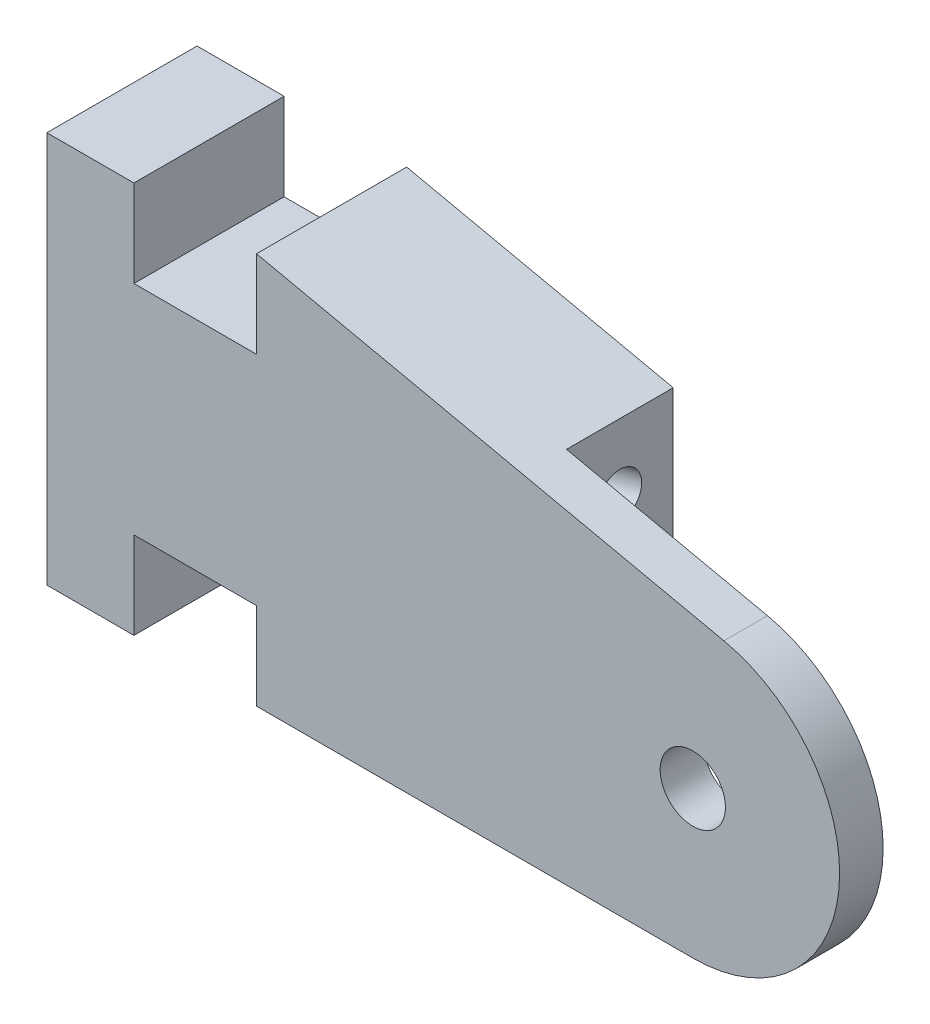
SolidWorks part; units mm, degrees
ref_plane "Front Plane" through (0, 0, 0) normal (0, 0, 1) x (1, 0, 0)
ref_plane "Top Plane" through (0, 0, 0) normal (0, 1, 0) x (1, 0, 0)
ref_plane "Right Plane" through (0, 0, 0) normal (1, 0, 0) x (0, 0, -1)
sketch "Sketch1" plane through (0, 0, 0) normal (0, 0, 1) x (1, 0, 0)
  line L0 (0, 0) -> (0, 18.0003)
  line L1 (9.6315, 0) -> (9.6315, 4)
  line L2 (9.6315, 4) -> (4, 4)
  line L3 (9.6315, 18.0003) -> (31.1079, 13.3365)
  line L4 (9.6315, 18.0003) -> (9.6315, 14.0003)
  line L5 (9.6315, 14.0003) -> (4, 14.0003)
  line L6 (0, 0) -> (4, 0)
  line L7 (4, 0) -> (4, 4)
  line L9 (14.2505, 12.0256) -> (12.2808, 11.6783) construction
  line L10 (7.3568, 10.81) -> (8.225, 5.886) construction
  line L11 (7.3568, 10.81) -> (5.3872, 10.4627) construction
  line L12 (4, 18.0003) -> (4, 14.0003)
  line L13 (0, 18.0003) -> (4, 18.0003)
  line L14 (5.3872, 10.4627) -> (6.2554, 5.5387) construction
  line L15 (6.2554, 5.5387) -> (8.225, 5.886) construction
  line L16 (12.2808, 11.6783) -> (13.1491, 6.7542) construction
  line L17 (13.1491, 6.7542) -> (15.1187, 7.1015) construction
  line L18 (14.2505, 12.0256) -> (15.1187, 7.1015) construction
  line L20 (9.6315, 0) -> (29.6765, 0)
  circle A0 centre (29.6765, 6.745) radius 12.12 construction
  arc A1 (29.6765, 0) -> (31.1079, 13.3365) centre (29.6765, 6.745) ccw
  circle A5 centre (29.6765, 6.745) radius 1.5
  dimension "D1" = 3
  dimension "D2" = 6.745
  dimension "D12" = 24.24
  dimension "D4" = 5.3872
  dimension "D5" = 6.2554
  dimension "D6" = 7.3568
  dimension "D7" = 12.2808
  dimension "D8" = 18.0003
  dimension "D9" = 5.6315
  dimension "D10" = 5.5387
  dimension "D11" = 5.886
  dimension "D13" = 9.6315
  dimension "ThumbLinkLengthMCP" = 20.045
extrude "Boss-Extrude1" add sketch "Sketch1" along normal blind 6.9
sketch "Sketch4" plane through (0, 0, 0) normal (0, 0, 1) x (1, 0, 0)
  line L0 (21.8765, 0) -> (21.8765, 15.3412)
  line L2 (21.8765, 0) -> (29.6765, 0)
  line L3 (9.6315, 0) -> (29.6765, 0) construction
  line L4 (31.1079, 13.3365) -> (9.6315, 18.0003) construction
  line L5 (21.8765, 15.3412) -> (31.1079, 13.3365)
  arc A0 (29.6765, 0) -> (31.1079, 13.3365) centre (29.6765, 6.745) ccw
  dimension "D1" = 21.8765
extrude "Cut-Extrude2" cut sketch "Sketch4" along normal blind 4.9
sketch "Sketch5" plane through (0, 0, 0) normal (-1, 0, 0) x (0, 0, 1)
  line L0 (3.45, 0) -> (3.45, 18.0003) construction
  line L1 (6.9, 0) -> (0, 0) construction
  line L2 (6.9, 18.0003) -> (0, 18.0003) construction
  circle A0 centre (4.45, 8) radius 1 construction
  circle A1 centre (2.45, 8) radius 1
  dimension "D1" = 4.45
  dimension "D3" = 2
  dimension "D2" = 8
extrude "Cut-Extrude3" cut sketch "Sketch5" against normal blind 7
ref_plane "Plane1" through (24.2463, 6.4968, 0) normal (0.9659, 0.2588, 0) x (0, 0, -1)
sketch "Sketch8" plane through (24.2463, 6.4968, 0) normal (0.9659, 0.2588, 0) x (0, 0, -1)
  line L0 (-4.9, -5.662) -> (0, -5.662) construction
  line L1 (-4.9, -5.662) -> (0, -5.662) construction
  line L2 (-2.45, -5.662) -> (-2.45, 6.2012) construction
  circle A0 centre (-2.45, 6.2012) radius 1
  dimension "D1" = 2
  dimension "D2" = 6.2012
  dimension "D3" = 2.45
extrude "Cut-Extrude5" cut sketch "Sketch8" against normal blind 17
equation "\"ThumbLinkLengthMCP@Sketch1\"= \"HB@parametersSketch@prostheticParameters.SLDPRT\" * 0.211"
